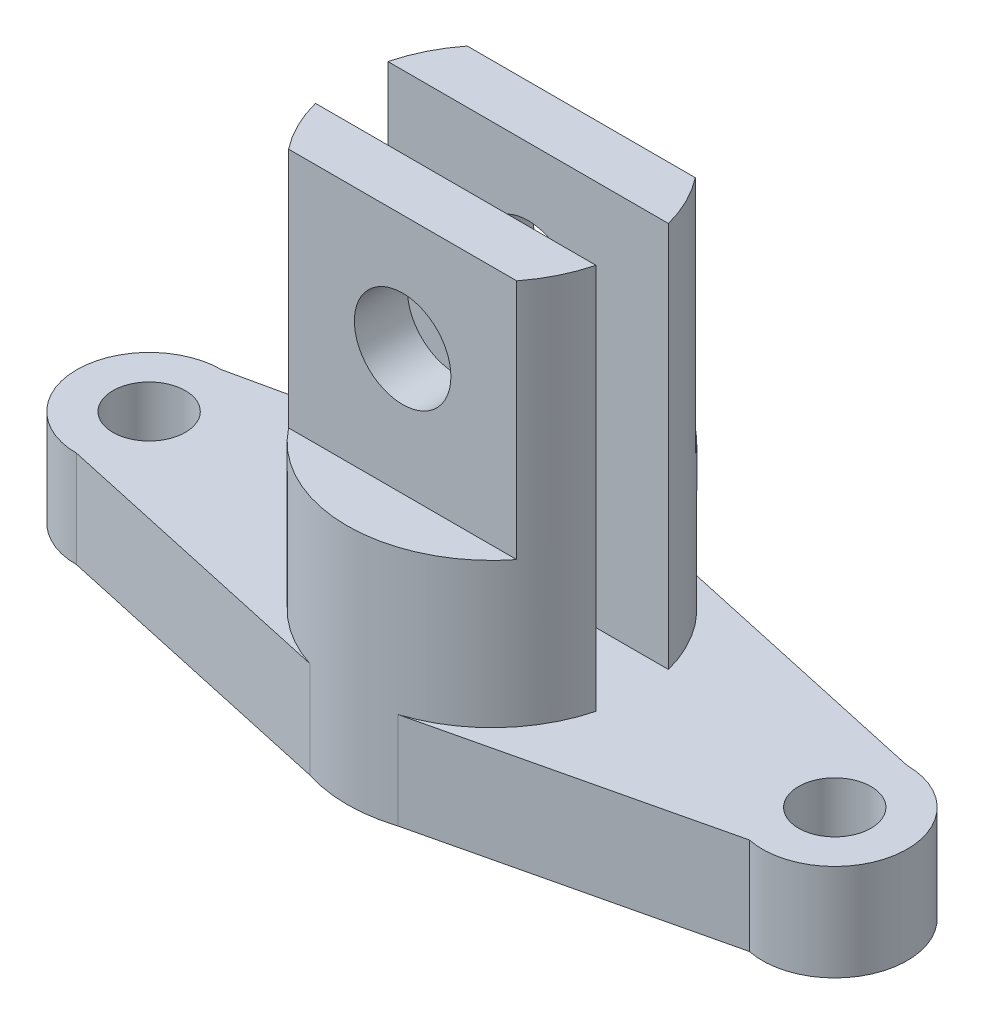
SolidWorks part; units mm, degrees
ref_plane "Front Plane" through (0, 0, 0) normal (0, 0, 1) x (1, 0, 0)
ref_plane "Top Plane" through (0, 0, 0) normal (0, 1, 0) x (1, 0, 0)
ref_plane "Right Plane" through (0, 0, 0) normal (1, 0, 0) x (0, 0, -1)
sketch "Sketch1" plane through (0, 0, 0) normal (0, 1, 0) x (1, 0, 0)
  line L1 (-49.86, -23.435) -> (11.986, -37.0043)
  line L2 (-49.86, 6.565) -> (11.986, 20.1343)
  line L3 (92.14, 6.565) -> (30.294, 20.1343)
  line L4 (89.1312, -23.1301) -> (30.294, -37.0043)
  arc A0 (-49.86, 6.565) -> (-49.86, -23.435) centre (-49.86, -8.435) ccw
  arc A1 (89.1312, -23.1301) -> (92.14, 6.565) centre (92.14, -8.435) ccw
  arc A2 (11.986, -37.0043) -> (30.294, -37.0043) centre (21.14, -8.435) ccw
  arc A3 (30.294, 20.1343) -> (11.986, 20.1343) centre (21.14, -8.435) ccw
  circle A4 centre (-49.86, -8.435) radius 7.5
  circle A5 centre (92.14, -8.435) radius 7.5
extrude "Boss-Extrude1" add sketch "Sketch1" along normal blind 20
sketch "Sketch2" plane through (0, 0, 0) normal (0, 1, 0) x (1, 0, 0)
  line L0 (-7.9074, -0.935) -> (50.1874, -0.935)
  line L2 (50.1874, -15.935) -> (-7.9074, -15.935)
  arc A0 (-7.9074, -15.935) -> (50.1874, -15.935) centre (21.14, -8.435) ccw
  arc A1 (50.1874, -0.935) -> (-7.9074, -0.935) centre (21.14, -8.435) ccw
extrude "Boss-Extrude2" add sketch "Sketch2" along normal blind 100
sketch "Sketch3" plane through (0, 100, 0) normal (0, 1, 0) x (1, 0, 0)
  line L1 (-2.4768, -26.935) -> (44.7567, -26.935)
  line L4 (44.7567, 10.065) -> (-2.4768, 10.065)
  arc A1 (-2.4768, -26.935) -> (44.7567, -26.935) centre (21.14, -8.435) ccw
  arc A5 (44.7567, 10.065) -> (-2.4768, 10.065) centre (21.14, -8.435) ccw
extrude "Cut-Extrude1" cut sketch "Sketch3" against normal blind 50 contours A5 L4 | A1 L1
sketch "Sketch4" plane through (0, 0, 26.935) normal (0, 0, 1) x (1, 0, 0)
  circle A0 centre (21.14, 76) radius 10
extrude "Cut-Extrude2" cut sketch "Sketch4" against normal blind 119 and the other way blind 30
